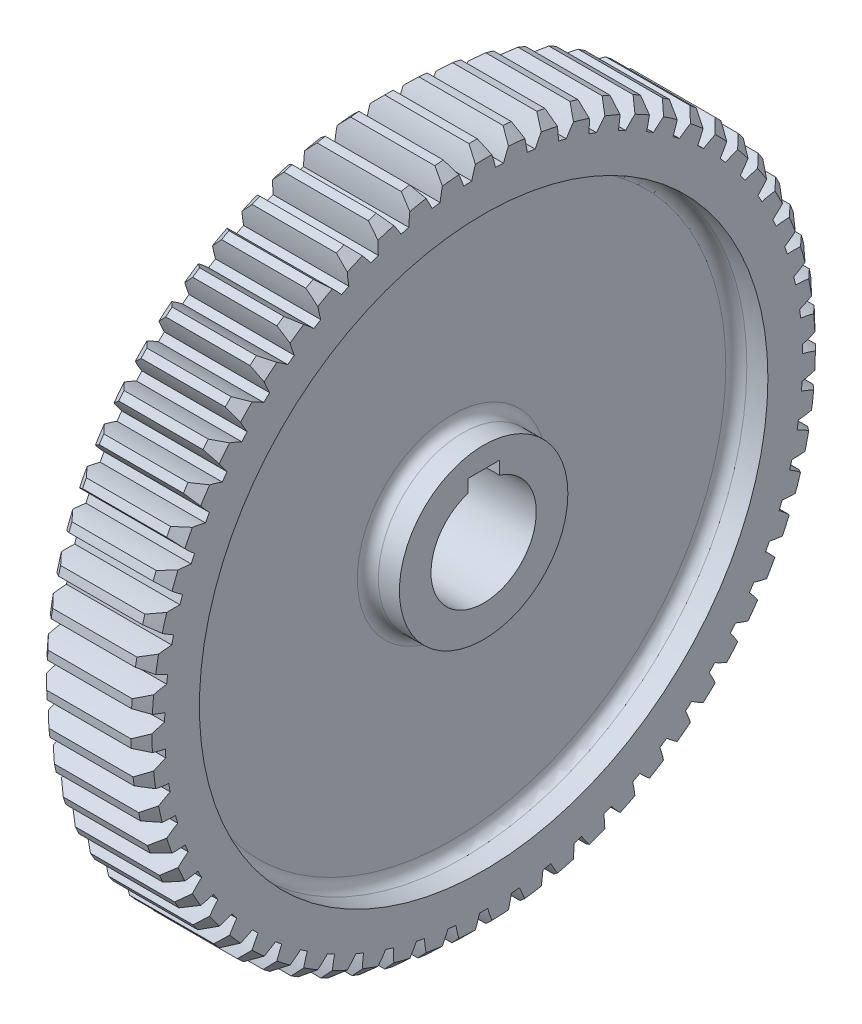
SolidWorks part; units mm, degrees
material "Сталь ШХ15 ГОСТ 801-78"
ref_plane "Plane1" through (0, 0, 0) normal (0, 0, 1) x (1, 0, 0)
ref_plane "Plane2" through (0, 0, 0) normal (0, 1, 0) x (1, 0, 0)
ref_plane "Plane3" through (0, 0, 0) normal (1, 0, 0) x (0, 0, -1)
sketch "Эскиз1" plane through (0, 0, 0) normal (0, 0, 1) x (1, 0, 0)
  line L0 (0, 0) -> (-28.3543, 0) construction
  line L1 (-10, 10) -> (10, 10)
  line L2 (10, 10) -> (10, 16)
  line L3 (10, 65) -> (-10, 65)
  line L4 (-10, 65) -> (-10, 54)
  line L5 (0, 10) -> (0, 0) construction
  line L6 (10, 54) -> (4, 54)
  line L7 (4, 54) -> (4, 16)
  line L8 (4, 16) -> (10, 16)
  line L9 (-10, 54) -> (-4, 54)
  line L10 (-4, 54) -> (-4, 16)
  line L11 (-4, 16) -> (-10, 16)
  line L12 (-10, 16) -> (-10, 10)
  line L13 (10, 54) -> (10, 65)
  dimension "D1" = 20
  dimension "D2" = 130
  dimension "D3" = 20
  dimension "D4" = 8
  dimension "D5" = 32
  dimension "D6" = 108
revolve "Повернуть1" add sketch "Эскиз1" angle 360 about L0
chamfer "Фаска1" distance 2 angle 45 2 edges at (10, 0, -65) (-10, 0, -65)
sketch "Sketch3" plane through (10, 9.4978, -4.3364) normal (1, 0, 0) x (0, 0, -1)
  line L0 (-4.3364, -9.4978) -> (-1.0965, 55.4214) construction
  line L1 (-4.3364, -9.4978) -> (58.6636, -9.4978) construction
  line L2 (58.6636, -9.4978) -> (60.6636, -9.4978) construction
  line L3 (-2.7658, 53.4826) -> (-4.3364, -9.4978) construction
  line L4 (-4.3364, -9.4978) -> (-4.3364, 6.5022) construction
  line L5 (-2.7658, 53.4826) -> (-1.1664, 54.02) construction
  line L6 (60.6636, -9.4978) -> (61.6636, -9.4978) construction
  line L7 (61.6636, -9.4978) -> (60.6636, -7.4978) construction
  line L8 (61.6636, -7.4978) -> (61.6636, -9.4978) construction
  circle A0 centre (-4.3364, -9.4978) radius 63 construction
  circle A1 centre (-4.3364, -9.4978) radius 63 construction
  circle A2 centre (-4.3364, -9.4978) radius 60.6 construction
  arc A3 (-2.0845, 51.0603) -> (-3.5402, 55.4973) centre (-26.6536, 45.4567) ccw
  arc A5 (1.3427, 55.2536) -> (-3.5402, 55.4973) centre (-4.3364, -9.4978) ccw
  arc A6 (-0.5476, 50.9836) -> (-2.0845, 51.0603) centre (-4.3364, -9.4978) ccw
  arc A7 (1.3427, 55.2536) -> (-0.5476, 50.9836) centre (23.3415, 42.9616) ccw
  dimension "D6" = 25.2
  dimension "D3" = 2.857
  dimension "D4" = 1.429
  dimension "D5" = 70
  dimension "D7" = 87.143
  dimension "Смещение_плюс_один" = 1
  dimension "Коэфф_уравнительного_смещения_плюс_один" = 1
extrude "Cut-Extrude1-Впадина зуба" cut sketch "Sketch3" against normal blind 50
pattern_circular "CirPattern2" count 63 over 360 about axis through (0, 0, 0) along (1, 0, 0) of "Cut-Extrude1-Впадина зуба"
other "Зубчатый венец<1>"
fillet "Скругление1" radius 2 4 edges at (4, 0, -16) (4, 0, -54) (-4, 0, -54) (-4, 0, -16)
sketch "Эскиз3" plane through (0, 0, 0) normal (1, 0, 0) x (0, 0, -1)
  line L1 (3, 0) -> (-3, 0)
  line L2 (3, 0) -> (3, 12)
  line L3 (3, 12) -> (-3, 12)
  line L4 (-3, 0) -> (-3, 12)
  dimension "D1" = 6
  dimension "D2" = 12
extrude "Вырез-Вытянуть1" cut sketch "Эскиз3" against normal through all both and the other way through all
equation "\"Средний@Sketch3\" = \"Делительный@Sketch3\" + 2 * \"D0_модуль@Sketch3\" *  ( \"Смещение_плюс_один@Sketch3\" - 1 ) "
equation "\"D1@CirPattern2\" = \"D0_число_зубьев@Sketch3\""
equation "\"Диаметр_вершин@Sketch3\" = \"Средний@Sketch3\" + 2 * ( \"D0_модуль@Sketch3\" - ( \"Коэфф_уравнительного_смещения_плюс_один@Sketch3\" - 1 ) )"
equation "\"Диаметр_впадин@Sketch3\" = \"Средний@Sketch3\" - 2.4 * \"D0_модуль@Sketch3\""
equation "\"D3@Sketch3\" = 180 / \"D0_число_зубьев@Sketch3\""
equation "\"D4@Sketch3\" = 90 / \"D0_число_зубьев@Sketch3\""
equation "\"Делительный@Sketch3\"= \"D0_число_зубьев@Sketch3\" * \"D0_модуль@Sketch3\""
equation "\"D6@Sketch3\" = \"D0_число_зубьев@Sketch3\" * \"D0_модуль@Sketch3\" / 5"
